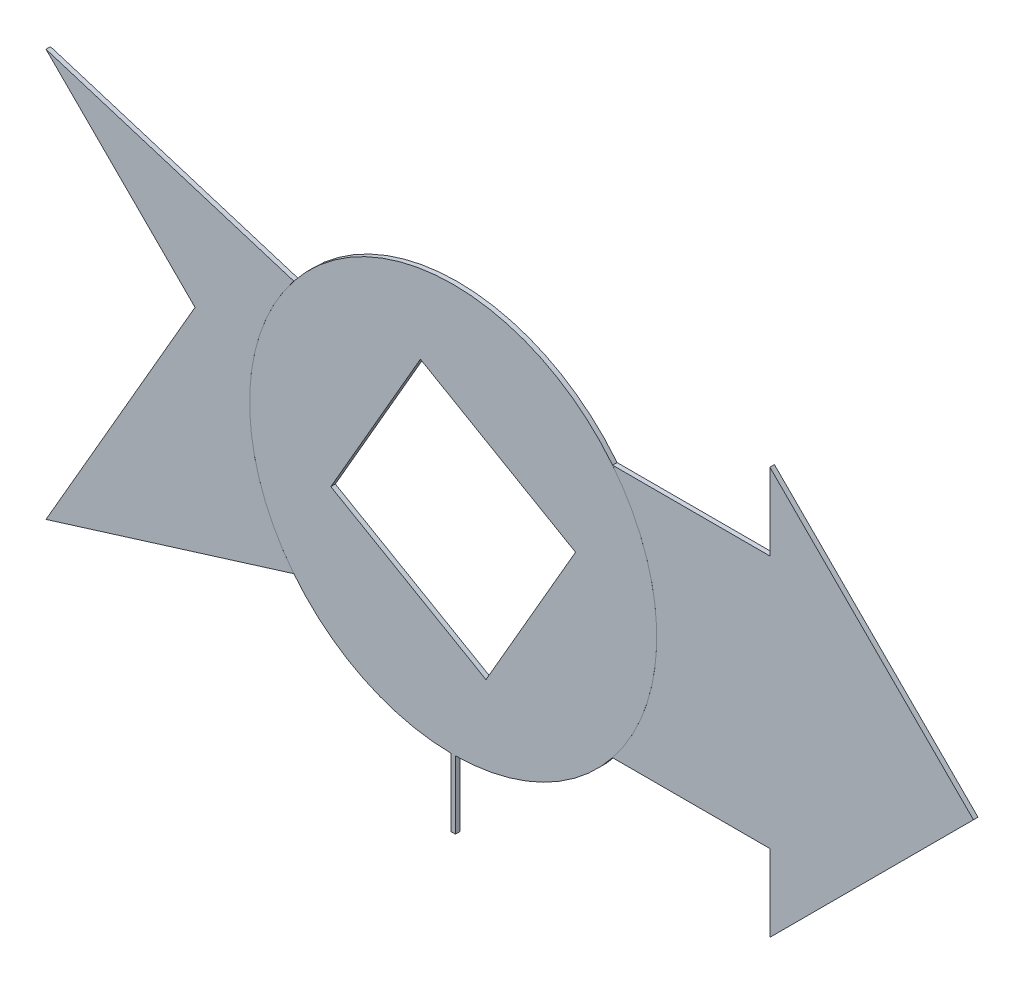
SolidWorks part; units mm, degrees
ref_plane "Front Plane" through (0, 0, 0) normal (0, 0, 1) x (1, 0, 0)
ref_plane "Top Plane" through (0, 0, 0) normal (0, 1, 0) x (1, 0, 0)
ref_plane "Right Plane" through (0, 0, 0) normal (1, 0, 0) x (0, 0, -1)
sketch "Sketch1" plane through (0, 0, 0) normal (0, 0, 1) x (1, 0, 0)
  line L2 (89.5, 15.0028) -> (89.5, 0)
  line L3 (89.5, 0) -> (90.5, 0)
  line L4 (90.5, 15.0028) -> (90.5, 0)
  arc A0 (90.5, 15.0028) -> (89.5, 15.0028) centre (90, 60) ccw
  dimension "D2" = 90
  dimension "D1" = 90
  dimension "D3" = 60
  dimension "D4" = 1
  dimension "D5" = 0.5
extrude "Central circle" add sketch "Sketch1" along normal blind 1
sketch "Sketch2" plane through (0, 0, 0) normal (0, 0, 1) x (1, 0, 0)
  line L0 (0, 15) -> (54.7722, 32)
  line L1 (0, 15) -> (32.9423, 72.0577)
  line L2 (32.9423, 72.0577) -> (0, 105)
  line L3 (0, 105) -> (54.7722, 88)
  line L4 (0, 0) -> (0, 144.1016) construction
  line L8 (89.5, 15.0028) -> (89.5, 0)
  line L10 (89.5, 0) -> (90.5, 0)
  line L12 (90.5, 0) -> (90.5, 15.0028)
  circle A0 centre (90, 60) radius 45 construction
  arc A2 (90.5, 15.0028) -> (89.5, 15.0028) centre (90, 60) ccw
  arc A3 (54.7722, 88) -> (54.7722, 32) centre (90, 60) ccw
  dimension "D1" = 30
  dimension "D2" = 45
  dimension "D3" = 15
  dimension "D4" = 32
  dimension "D6" = 90
  dimension "D7" = 56
  dimension "D5" = 0
extrude "Back of arrow" add sketch "Sketch2" along normal blind 1 separate body
sketch "Sketch3" plane through (0, 0, 0) normal (0, 0, 1) x (1, 0, 0)
  line L0 (160, 105) -> (205, 60)
  line L1 (205, 60) -> (160, 15)
  line L2 (160, 15) -> (160, 32)
  line L3 (160, 32) -> (125.2278, 32)
  line L4 (160, 105) -> (160, 88)
  line L5 (160, 88) -> (125.2278, 88)
  line L9 (89.5, 15.0028) -> (89.5, 0)
  line L11 (89.5, 0) -> (90.5, 0)
  line L13 (90.5, 0) -> (90.5, 15.0028)
  arc A1 (90.5, 15.0028) -> (89.5, 15.0028) centre (90, 60) ccw
  arc A2 (125.2278, 32) -> (125.2278, 88) centre (90, 60) ccw
  dimension "D2" = 17
  dimension "D3" = 90
  dimension "D4" = 70
  dimension "D1" = 0
extrude "Front of arrow" add sketch "Sketch3" along normal blind 1 separate body contours L1 L2 L3 A2 L5 L4 L0
sketch "Sketch4" plane through (0, 0, 1) normal (0, 0, 1) x (1, 0, 0)
  line L0 (62.9541, 52.7531) -> (97.2469, 32.9541)
  line L1 (62.9541, 52.7531) -> (82.7531, 87.0459)
  line L2 (97.2469, 32.9541) -> (117.0459, 67.2469)
  line L3 (82.7531, 87.0459) -> (117.0459, 67.2469)
  line L4 (97.2469, 32.9541) -> (125.9655, 32.9541) construction
  circle A0 centre (90, 60) radius 45 construction
  circle A1 centre (90, 60) radius 28 construction
  dimension "D2" = 56
  dimension "D1" = 60
extrude "Square hole" cut sketch "Sketch4" against normal blind 1
equation "\"D4@Sketch2\"=15+(45-28)"
equation "\"D2@Sketch3\"=45-28"
